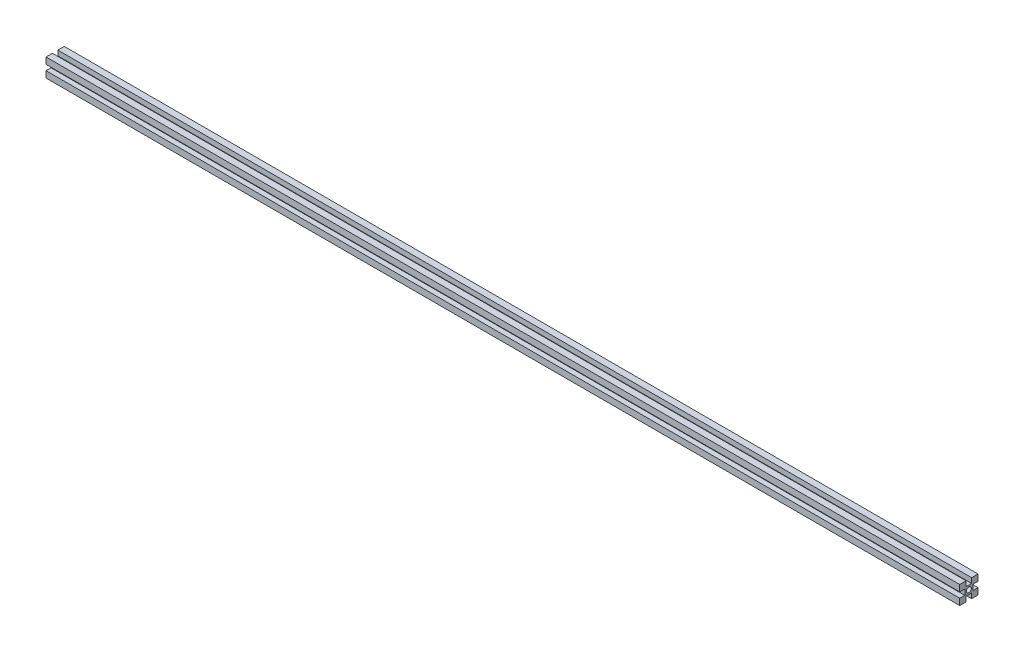
SolidWorks part; units mm, degrees
ref_plane "Plan de face" through (0, 0, 0) normal (0, 0, 1) x (1, 0, 0)
ref_plane "Plan de dessus" through (0, 0, 0) normal (0, 1, 0) x (1, 0, 0)
ref_plane "Plan de droite" through (0, 0, 0) normal (1, 0, 0) x (0, 0, -1)
ref_plane "Plan4" through (0, 0, 0) normal (-1, 0, 0) x (0, -1, 0)
sketch "Esquisse1" plane through (0, 0, 0) normal (-1, 0, 0) x (0, -1, 0)
  line L0 (-3, -10) -> (-3, -4.5)
  line L1 (-3, -4.5) -> (3, -4.5)
  line L2 (3, -4.5) -> (3, -10)
  line L3 (3, -10) -> (10, -10)
  line L4 (10, -10) -> (10, -3)
  line L5 (10, -3) -> (4.5, -3)
  line L6 (4.5, -3) -> (4.5, 3)
  line L7 (4.5, 3) -> (10, 3)
  line L8 (10, 3) -> (10, 10)
  line L9 (10, 10) -> (3, 10)
  line L10 (3, 10) -> (3, 4.5)
  line L11 (3, 4.5) -> (-3, 4.5)
  line L12 (-3, 4.5) -> (-3, 10)
  line L13 (-3, 10) -> (-10, 10)
  line L14 (-10, 10) -> (-10, 3)
  line L15 (-10, 3) -> (-4.5, 3)
  line L16 (-4.5, 3) -> (-4.5, -3)
  line L17 (-4.5, -3) -> (-10, -3)
  line L18 (-10, -3) -> (-10, -10)
  line L19 (-10, -10) -> (-3, -10)
  circle A0 centre (0, 0) radius 2.75
extrude "Boss.-Extru.1" add sketch "Esquisse1" against normal blind 1000
